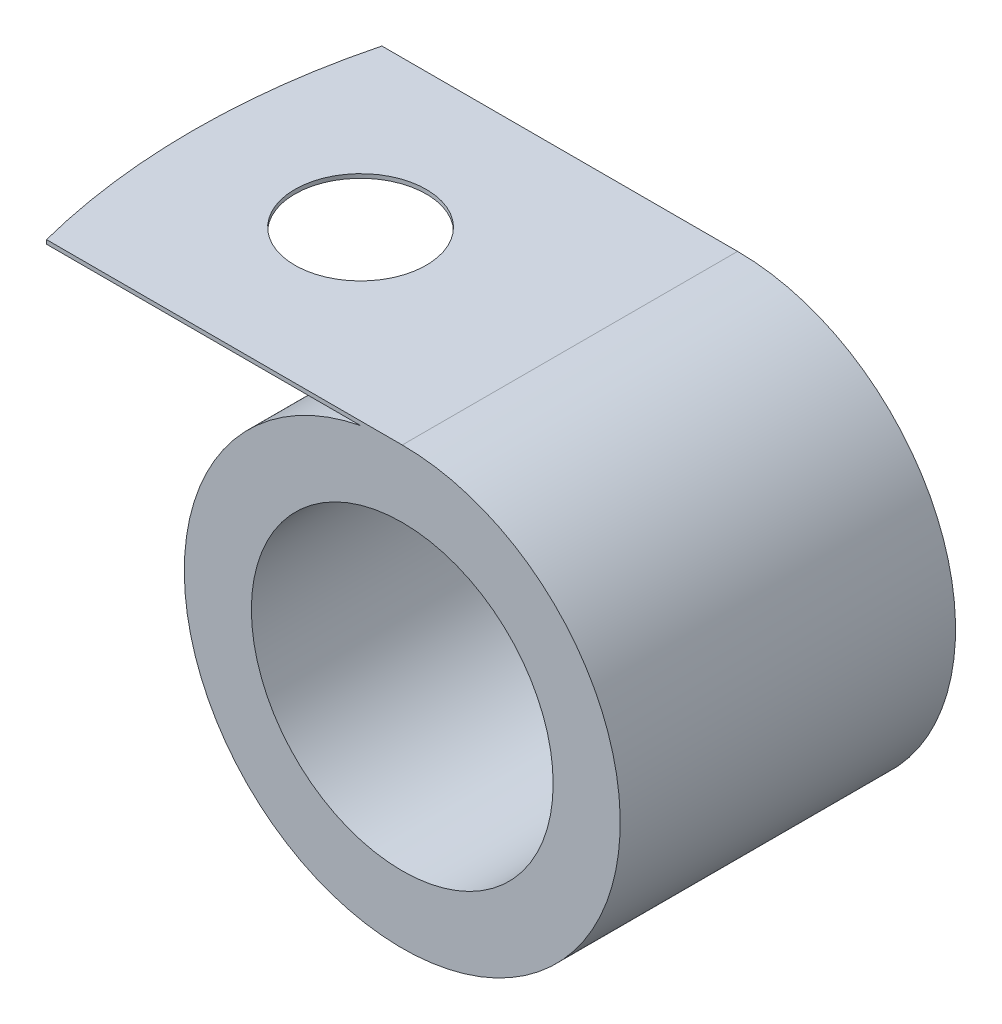
SolidWorks part; units mm, degrees
ref_plane "Front Plane" through (0, 0, 0) normal (0, 0, 1) x (1, 0, 0)
ref_plane "Top Plane" through (0, 0, 0) normal (0, 1, 0) x (1, 0, 0)
ref_plane "Right Plane" through (0, 0, 0) normal (1, 0, 0) x (0, 0, -1)
sketch "Sketch1" plane through (0, 0, 0) normal (0, 0, 1) x (1, 0, 0)
  line L0 (0, 8.255) -> (-14.2789, 8.255)
  line L1 (-14.2789, 8.255) -> (-14.2789, 8.1026)
  line L2 (-14.2789, 8.1026) -> (-1.5789, 8.1026)
  circle A0 centre (0, 0) radius 5.715
  arc A1 (-1.5789, 8.1026) -> (0, 8.255) centre (0, 0) ccw
  dimension "D1" = 11.43
  dimension "D2" = 16.51
  dimension "D3" = 12.7
  dimension "D4" = 0.1524
extrude "Boss-Extrude1" add sketch "Sketch1" along normal mid plane 12.7
sketch "Sketch2" plane through (0, 8.255, 0) normal (0, 1, 0) x (1, 0, 0)
  line L0 (0, 6.35) -> (-14.2789, 6.35) construction
  line L1 (0, -6.35) -> (-14.2789, -6.35) construction
  line L2 (-14.2789, -6.35) -> (-14.2789, 6.35) construction
  line L7 (0, 6.35) -> (-14.2789, 6.35)
  line L8 (-14.2789, 6.35) -> (-14.2789, -6.35)
  line L9 (-14.2789, -6.35) -> (0, -6.35)
  line L10 (0, -6.35) -> (0, 6.35)
  line L11 (-13.4723, 6.35) -> (-14.2789, 6.35)
  line L12 (-14.2789, 6.35) -> (-14.2789, -6.35)
  line L13 (-14.2789, -6.35) -> (-13.4723, -6.35)
  arc A0 (-13.4723, 6.35) -> (-13.4723, -6.35) centre (11.1211, 0) ccw
  circle A1 centre (-7.9289, 0) radius 2.4892
  line M5 (0, 6.35) -> (-14.2789, 6.35)
  line M6 (-14.2789, 6.35) -> (-14.2789, -6.35)
  line M7 (-14.2789, -6.35) -> (0, -6.35)
  dimension "D1" = 25.4
  dimension "D3" = 4.9784
  dimension "D4" = 6.35
  dimension "D2" = 0
extrude "Cut-Extrude1" cut sketch "Sketch2" against normal up to next contours A1 | A0 M5 M6 | A0 L12 M7
